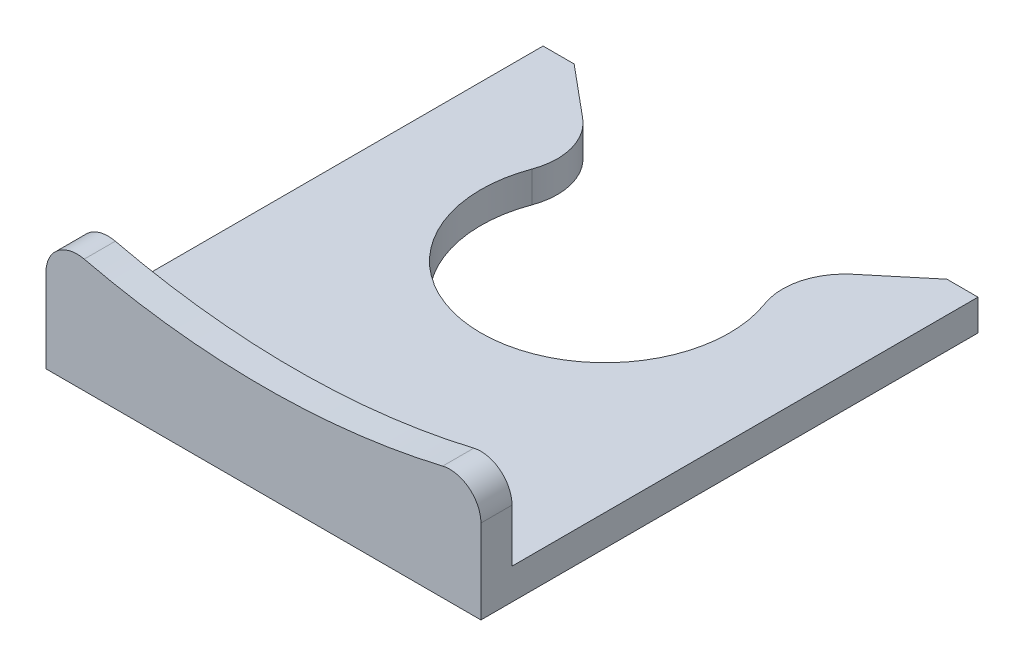
SolidWorks part; units mm, degrees
ref_plane "Front Plane" through (0, 0, 0) normal (0, 0, 1) x (1, 0, 0)
ref_plane "Top Plane" through (0, 0, 0) normal (0, 1, 0) x (1, 0, 0)
ref_plane "Right Plane" through (0, 0, 0) normal (1, 0, 0) x (0, 0, -1)
sketch "Sketch1" plane through (0, 0, 0) normal (0, 1, 0) x (1, 0, 0)
  line L0 (-7, -8) -> (7, 8) construction
  line L1 (-7, 8) -> (-6, 8)
  line L2 (-7, 8) -> (-7, -8)
  line L3 (-7, -8) -> (7, -8)
  line L4 (7, 8) -> (7, -8)
  line L5 (4.3457, 6.6214) -> (6, 8)
  line L6 (-4.3457, 6.6214) -> (-6, 8)
  line L7 (6, 8) -> (7, 8)
  line L8 (0, 3) -> (3.0729, 5.5607) construction
  line L9 (0, 3) -> (-3.0729, 5.5607) construction
  arc A0 (-3.7507, 4.39) -> (3.7507, 4.39) centre (0, 3) ccw
  arc A1 (-4.3457, 6.6214) -> (-3.7507, 4.39) centre (-5.6261, 5.085) cw
  arc A2 (4.3457, 6.6214) -> (3.7507, 4.39) centre (5.6261, 5.085) ccw
  dimension "D3" = 8
  dimension "D7" = 2
  dimension "D1" = 16
  dimension "D2" = 14
  dimension "D4" = 7
  dimension "D5" = 1
  dimension "D6" = 1
extrude "Extrude1" add sketch "Sketch1" along normal blind 1
sketch "Sketch2" plane through (0, 0, 8) normal (0, 0, 1) x (1, 0, 0)
  line L0 (7, 1) -> (7, 0) construction
  line L1 (-7, 0) -> (7, 0)
  line L2 (-7, 0) -> (-7, 4)
  line L3 (-7, 4) -> (7, 4) construction
  line L4 (7, 0) -> (7, 4)
  line L5 (-7, 0) -> (7, 0) construction
  arc A0 (-7, 4) -> (7, 4) centre (0, 28) ccw
  dimension "D2" = 3
  dimension "D1" = 4
extrude "Extrude2" add sketch "Sketch2" against normal blind 1
fillet "Fillet1" radius 1 2 edges at (7, 4, 7.5) (-7, 4, 7.5)
